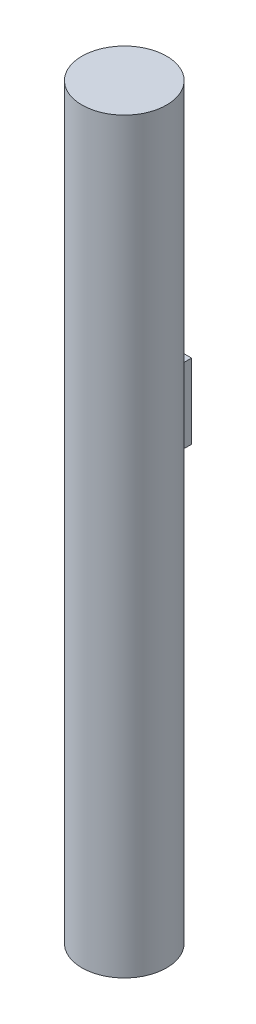
SolidWorks part; units mm, degrees
material "Stainless Steel (ferritic)"
ref_plane "Front Plane" through (0, 0, 0) normal (0, 0, 1) x (1, 0, 0)
ref_plane "Top Plane" through (0, 0, 0) normal (0, 1, 0) x (1, 0, 0)
ref_plane "Right Plane" through (0, 0, 0) normal (1, 0, 0) x (0, 0, -1)
sketch "Sketch1" plane through (0, 0, 0) normal (0, 1, 0) x (1, 0, 0)
  circle A0 centre (0, 0) radius 8.5
  dimension "D1" = 17
extrude "Boss-Extrude1" add sketch "Sketch1" along normal blind 150
ref_plane "Plane1" through (0, 82.02, 0) normal (0, 1, 0) x (1, 0, 0)
sketch "Sketch5" plane through (0, 82.02, 0) normal (0, 1, 0) x (1, 0, 0)
  line L1 (-2, 0) -> (2, 0)
  line L2 (-2, 0) -> (-2, 11.5)
  line L3 (-2, 11.5) -> (2, 11.5)
  line L4 (2, 0) -> (2, 11.5)
  point P4 (0, 0)
  dimension "D1" = 11.5
  dimension "D2" = 4
extrude "Boss-Extrude2" add sketch "Sketch5" along normal blind 15 contours L4 L3 L2 L1
fillet "Fillet1" radius 1.5 4 edges at (0, 82.02, -8.5) (2, 89.52, -8.2614) (0, 97.02, -8.5) (-2, 89.52, -8.2614)
